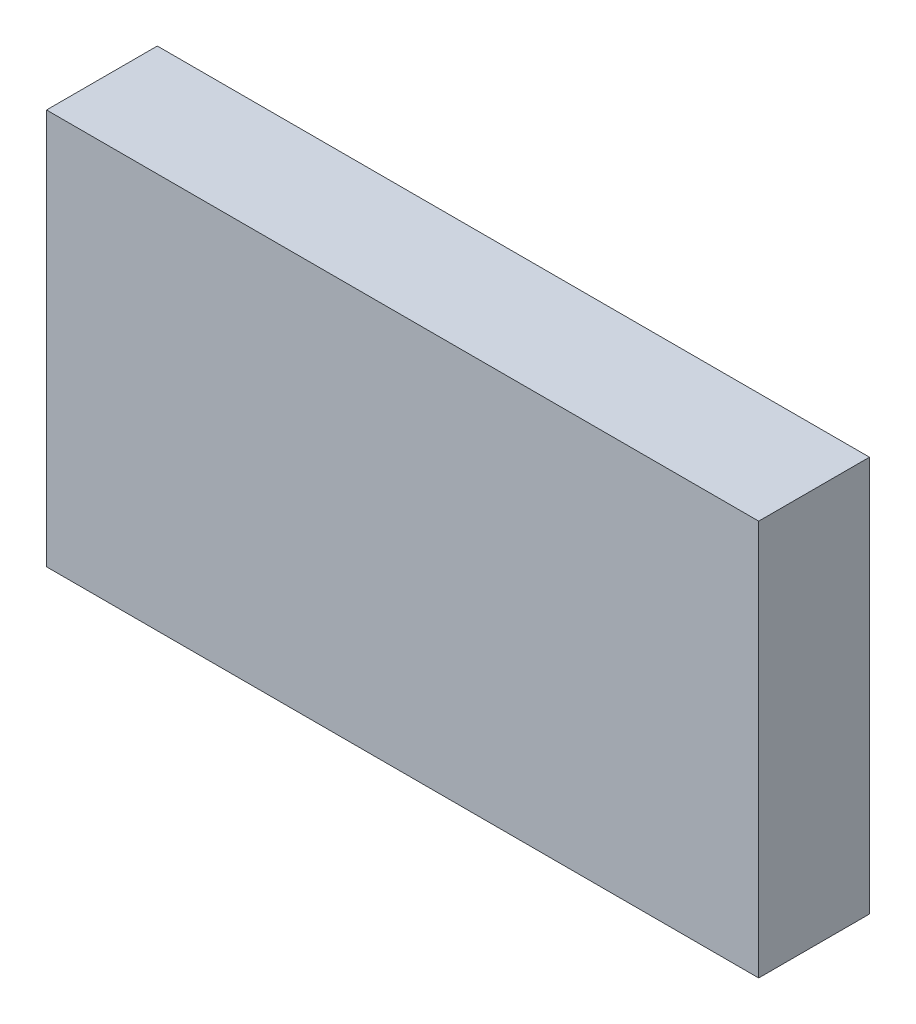
SolidWorks part; units mm, degrees
material "Pine"
ref_plane "Front Plane" through (0, 0, 0) normal (0, 0, 1) x (1, 0, 0)
ref_plane "Top Plane" through (0, 0, 0) normal (0, 1, 0) x (1, 0, 0)
ref_plane "Right Plane" through (0, 0, 0) normal (1, 0, 0) x (0, 0, -1)
sketch "Sketch1" plane through (0, 0, 0) normal (0, 0, 1) x (1, 0, 0)
  line L0 (8932.6508, -5243.5125) -> (10226.1458, -5243.5125)
  line L1 (9086.3208, -4722.0918) -> (10222.9708, -4853.7812)
  line L2 (8914.8708, -6342.0625) -> (10197.5708, -6342.0625)
  line L3 (8914.8708, -5808.6625) -> (10197.5708, -5808.6625)
  line L4 (8919.6333, -5253.0375) -> (10218.2083, -5253.0375)
  line L5 (9134.2633, -4656.1375) -> (9134.2633, -4638.3575)
  line L6 (9091.0833, -4638.3575) -> (9134.2633, -4638.3575)
  line L7 (9091.0833, -4567.2375) -> (9091.0833, -4638.3575)
  line L8 (9134.2633, -4656.1375) -> (9581.3033, -4656.1375)
  line L9 (9091.0833, -4567.2375) -> (9624.4833, -4567.2375)
  line L10 (9581.3033, -4656.1375) -> (9581.3033, -4638.3575)
  line L11 (9581.3033, -4638.3575) -> (9624.4833, -4638.3575)
  line L12 (9624.4833, -4567.2375) -> (9624.4833, -4638.3575)
  line L13 (8932.6508, -5225.7325) -> (9344.9775, -5225.7325)
  line L14 (8932.6508, -5256.2125) -> (8932.6508, -5243.5125)
  line L15 (8911.6958, -5256.2125) -> (8932.6508, -5256.2125)
  line L16 (8914.8708, -4722.0918) -> (9086.3208, -4722.0918)
  line L17 (8911.6958, -4715.5913) -> (8932.6508, -4715.5913)
  line L18 (8914.8708, -6342.0625) -> (8914.8708, -5808.6625)
  line L19 (12082.9917, -4722.0918) -> (10946.3417, -4853.7812)
  line L20 (12236.6617, -5243.5125) -> (10943.1667, -5243.5125)
  line L21 (10951.1042, -5253.0375) -> (12249.6792, -5253.0375)
  line L22 (10838.3917, -5656.2625) -> (11308.2917, -5656.2625)
  line L23 (10838.3917, -5719.7625) -> (11308.2917, -5719.7625)
  line L24 (10838.3917, -5742.5368) -> (11308.2917, -5742.5368)
  line L25 (10806.6417, -6342.0625) -> (11340.0417, -6342.0625)
  line L26 (10803.4667, -6335.7125) -> (11343.2167, -6335.7125)
  line L27 (10803.4667, -6317.9325) -> (11343.2167, -6317.9325)
  line L28 (10943.1667, -5225.7325) -> (11376.4483, -5225.7325)
  line L29 (11506.7292, -4754.5625) -> (10806.6417, -4827.5875)
  line L30 (11506.7292, -4567.2375) -> (11506.7292, -4754.5625)
  line L31 (10806.6417, -4567.2375) -> (10806.6417, -4827.5875)
  line L32 (10806.6417, -4567.2375) -> (11506.7292, -4567.2375)
  line L33 (10235.6708, -6329.3625) -> (10245.1958, -6329.3625)
  line L34 (10245.1958, -6329.3625) -> (10254.7208, -6278.5625)
  line L35 (10302.3458, -6329.3625) -> (10311.8708, -6278.5625)
  line L36 (10302.3458, -6329.3625) -> (10292.8208, -6329.3625)
  line L37 (10245.1958, -5821.3625) -> (10254.7208, -5872.1625)
  line L38 (10235.6708, -5821.3625) -> (10245.1958, -5821.3625)
  line L39 (10292.8208, -5821.3625) -> (10302.3458, -5821.3625)
  line L40 (10302.3458, -5821.3625) -> (10311.8708, -5872.1625)
  line L41 (10235.6708, -5821.3625) -> (10235.6708, -6329.3625)
  line L42 (10254.7208, -5872.1625) -> (10254.7208, -6278.5625)
  line L43 (10311.8708, -5872.1625) -> (10311.8708, -6278.5625)
  line L44 (10292.8208, -5821.3625) -> (10292.8208, -6329.3625)
  line L45 (8932.6508, -5225.7325) -> (8932.6508, -4715.5913)
  line L46 (8911.6958, -4715.5913) -> (8911.6958, -5256.2125)
  line L47 (8914.8708, -5248.275) -> (8914.8708, -4722.0918)
  line L48 (8919.6333, -5253.0375) -> (8914.8708, -5248.275)
  line L49 (8914.8708, -5145.0875) -> (8937.426, -5145.0875)
  line L50 (8914.8708, -5202.2375) -> (8937.426, -5202.2375)
  line L51 (10838.3917, -5656.2625) -> (10838.3917, -5719.7625)
  line L52 (10832.0417, -5736.1868) -> (10856.1717, -5736.1868)
  line L53 (10806.6417, -6342.0625) -> (10806.6417, -5818.7368)
  line L54 (10832.0417, -5649.9125) -> (10856.1717, -5649.9125)
  line L55 (10832.0417, -5726.1125) -> (10856.1717, -5726.1125)
  line L56 (10806.6417, -5818.7368) -> (10833.9015, -5818.7368)
  line L57 (10832.0417, -5806.0442) -> (10851.6815, -5806.0442)
  line L58 (10856.1717, -5801.5541) -> (10856.1717, -5736.1868)
  line L59 (10838.3917, -5814.2467) -> (10838.3917, -5742.5368)
  line L60 (10832.0417, -5806.0442) -> (10832.0417, -5736.1868)
  line L61 (10803.4667, -6317.9325) -> (10803.4667, -6335.7125)
  line L62 (10197.5708, -5808.6625) -> (10197.5708, -6342.0625)
  line L63 (9762.3842, -6348.4125) -> (9762.3842, -5802.3125)
  line L64 (9780.1642, -6348.4125) -> (9762.3842, -6348.4125)
  line L65 (9780.1642, -5802.3125) -> (9780.1642, -6348.4125)
  line L66 (9762.3842, -5802.3125) -> (9780.1642, -5802.3125)
  line L67 (9332.2775, -6348.4125) -> (9332.2775, -5802.3125)
  line L68 (9332.2775, -6348.4125) -> (9350.0575, -6348.4125)
  line L69 (9350.0575, -5802.3125) -> (9350.0575, -6348.4125)
  line L70 (9332.2775, -5802.3125) -> (9350.0575, -5802.3125)
  line L71 (9993.8374, -6061.075) -> (9993.8374, -6045.2418)
  line L72 (9998.5999, -6065.8375) -> (10014.4331, -6065.8375)
  line L73 (9998.5999, -6084.8875) -> (10014.4331, -6084.8875)
  line L74 (9993.8374, -6105.4832) -> (9993.8374, -6089.65)
  line L75 (9974.7874, -6105.4832) -> (9974.7874, -6089.65)
  line L76 (9954.1917, -6084.8875) -> (9970.0249, -6084.8875)
  line L77 (9974.7874, -6061.075) -> (9974.7874, -6045.2418)
  line L78 (9954.1917, -6065.8375) -> (9970.0249, -6065.8375)
  line L79 (10793.9417, -6237.2875) -> (10816.4969, -6237.2875)
  line L80 (10793.9417, -6294.4375) -> (10816.4969, -6294.4375)
  line L81 (10856.1717, -5649.9125) -> (10856.1717, -5726.1125)
  line L82 (10832.0417, -5726.1125) -> (10832.0417, -5649.9125)
  line L83 (10226.1458, -5225.7325) -> (10226.1458, -5243.5125)
  line L84 (10205.1908, -5257.8) -> (10205.1908, -4844.2499)
  line L85 (10230.9083, -4844.2499) -> (10230.9083, -5257.8)
  line L86 (10205.1908, -5257.8) -> (10230.9083, -5257.8)
  line L87 (10205.1908, -4844.2499) -> (10230.9083, -4844.2499)
  line L88 (10946.3417, -5176.8375) -> (10968.8969, -5176.8375)
  line L89 (9349.4676, -5141.9125) -> (9358.2674, -5141.9125)
  line L90 (10946.3417, -5119.6875) -> (10968.8969, -5119.6875)
  line L91 (9929.011, -4660.9635) -> (10066.0807, -4660.9635)
  line L92 (9929.011, -4678.7435) -> (10066.0807, -4678.7435)
  line L93 (10943.1667, -5225.7325) -> (10943.1667, -5243.5125)
  line L94 (10946.3417, -5248.275) -> (10951.1042, -5253.0375)
  line L95 (10946.3417, -5257.8063) -> (10946.3417, -4849.0188)
  line L96 (10964.1217, -5257.8) -> (10964.1217, -4844.2499)
  line L97 (10938.4042, -4844.2499) -> (10938.4042, -5257.8)
  line L98 (10938.4042, -5257.8) -> (10964.1217, -5257.8)
  line L99 (10964.1217, -4844.2499) -> (10938.4042, -4844.2499)
  line L100 (10344.8908, -4560.8875) -> (10369.0208, -4560.8875)
  line L101 (10344.8908, -4560.8875) -> (10369.0208, -4560.8875)
  line L102 (10800.2917, -4560.8875) -> (10824.4217, -4560.8875)
  line L103 (10200.4156, -5119.6875) -> (10222.9708, -5119.6875)
  line L104 (10200.4156, -5176.8375) -> (10222.9708, -5176.8375)
  line L105 (9344.9775, -5146.4026) -> (9344.9775, -5225.7325)
  line L106 (10344.8908, -4560.8875) -> (10344.8908, -4833.9375)
  line L107 (9792.8642, -5225.7325) -> (9792.8642, -5146.4026)
  line L108 (9362.7575, -5225.7325) -> (9775.0842, -5225.7325)
  line L109 (9680.3633, -4761.8396) -> (9680.3633, -4559.9604)
  line L110 (9656.2333, -4559.9604) -> (9680.3633, -4559.9604)
  line L111 (9656.2333, -4761.8396) -> (9680.3633, -4761.8396)
  line L112 (9656.2333, -4761.8396) -> (9656.2333, -4559.9604)
  line L113 (9779.5743, -5141.9125) -> (9788.374, -5141.9125)
  line L114 (10070.5708, -4665.4536) -> (10070.5708, -4674.2534)
  line L115 (9924.5208, -4674.2534) -> (9924.5208, -4665.4536)
  line L116 (12127.4417, -6188.3925) -> (12205.5015, -6188.3925)
  line L117 (12209.9917, -6170.6125) -> (12209.9917, -6183.9024)
  line L118 (9792.8642, -5225.7325) -> (10226.1458, -5225.7325)
  line L119 (9662.5833, -4754.5625) -> (10362.6708, -4827.5875)
  line L120 (9662.5833, -4567.2375) -> (9662.5833, -4754.5625)
  line L121 (10362.6708, -4567.2375) -> (10362.6708, -4827.5875)
  line L122 (9662.5833, -4567.2375) -> (10362.6708, -4567.2375)
  line L123 (10824.4217, -4833.9375) -> (10800.2917, -4833.9375)
  line L124 (10800.2917, -4833.9375) -> (10800.2917, -4560.8875)
  line L125 (10824.4217, -4560.8875) -> (10824.4217, -4833.9375)
  line L126 (10344.8908, -4833.9375) -> (10369.0208, -4833.9375)
  line L127 (10369.0208, -4833.9375) -> (10369.0208, -4560.8875)
  line L128 (10222.9708, -5248.275) -> (10218.2083, -5253.0375)
  line L129 (10222.9708, -5257.8063) -> (10222.9708, -4849.0188)
  line L130 (11734.6544, -5701.375) -> (11739.2301, -5701.375)
  line L131 (9362.7575, -5225.7325) -> (9362.7575, -5146.4026)
  line L132 (9775.0842, -5146.4026) -> (9775.0842, -5225.7325)
  line L133 (11761.3864, -5701.375) -> (11756.8282, -5701.375)
  line L134 (11734.6544, -5693.755) -> (11739.2301, -5693.755)
  line L135 (11761.4039, -5693.755) -> (11756.8282, -5693.755)
  line L136 (11734.6544, -5701.375) -> (11739.2301, -5701.375)
  line L137 (11744.3462, -5721.3024) -> (11744.3462, -5706.4179)
  line L138 (11751.7122, -5721.3024) -> (11751.7122, -5706.4179)
  line L139 (11740.0917, -6170.6125) -> (11740.0917, -6183.9024)
  line L140 (11689.2917, -6188.3925) -> (11822.6417, -6188.3925)
  line L141 (11689.2917, -6348.4093) -> (11689.2917, -6164.2657)
  line L142 (11689.2917, -6164.2657) -> (11746.4417, -6164.2657)
  line L143 (11746.4417, -6164.2657) -> (11746.4417, -6188.3925)
  line L144 (11689.2917, -6164.2657) -> (11746.4417, -6164.2657)
  line L145 (11340.0417, -5818.7368) -> (11340.0417, -6342.0625)
  line L146 (11290.5117, -5726.1125) -> (11314.6417, -5726.1125)
  line L147 (11290.5117, -5649.9125) -> (11290.5117, -5726.1125)
  line L148 (11340.0417, -5818.7368) -> (11312.7818, -5818.7368)
  line L149 (11314.6417, -5806.0442) -> (11295.0018, -5806.0442)
  line L150 (11290.5117, -5801.5541) -> (11290.5117, -5736.1868)
  line L151 (11308.2917, -5814.2467) -> (11308.2917, -5742.5368)
  line L152 (11314.6417, -5806.0442) -> (11314.6417, -5736.1868)
  line L153 (11290.5117, -5736.1868) -> (11314.6417, -5736.1868)
  line L154 (11848.0417, -6267.1325) -> (11962.3417, -6267.1325)
  line L155 (11962.3417, -6267.1325) -> (11962.3417, -6203.6325)
  line L156 (11343.2167, -6317.9325) -> (11343.2167, -6335.7125)
  line L157 (11365.4417, -5656.2625) -> (11365.4417, -5719.7625)
  line L158 (11365.4417, -5656.2625) -> (11479.7417, -5656.2625)
  line L159 (11778.1917, -6071.3937) -> (11802.3217, -6071.3937)
  line L160 (11314.6417, -5726.1125) -> (11314.6417, -5649.9125)
  line L161 (11314.6417, -5649.9125) -> (11290.5117, -5649.9125)
  line L162 (11308.2917, -5719.7625) -> (11308.2917, -5656.2625)
  line L163 (11689.2917, -6348.4093) -> (11713.4217, -6348.4093)
  line L164 (12203.6417, -6164.2657) -> (12260.7917, -6164.2657)
  line L165 (11713.4217, -6348.4093) -> (11713.4217, -6164.2657)
  line L166 (11695.6417, -6342.0625) -> (11695.6417, -6170.6125)
  line L167 (11695.6417, -6048.5337) -> (11699.4517, -6052.3437)
  line L168 (11822.6417, -6292.5325) -> (11822.6417, -6188.3925)
  line L169 (11695.6417, -6342.0625) -> (11695.6417, -6170.6125)
  line L170 (11848.0417, -6203.6325) -> (11962.3417, -6203.6325)
  line L171 (11848.0417, -6203.6325) -> (11848.0417, -6267.1325)
  line L172 (11987.7417, -6267.1325) -> (11987.7417, -6203.6325)
  line L173 (11784.5417, -6077.7437) -> (11784.5417, -6141.2438)
  line L174 (11517.8417, -5656.2625) -> (11632.1417, -5656.2625)
  line L175 (11632.1417, -5656.2625) -> (11632.1417, -5719.7625)
  line L176 (11632.1417, -5719.7625) -> (11517.8417, -5719.7625)
  line L177 (11517.8417, -5719.7625) -> (11517.8417, -5656.2625)
  line L178 (11692.4667, -6028.2137) -> (11692.4667, -6045.9937)
  line L179 (11695.6417, -5979.3188) -> (11718.1969, -5979.3188)
  line L180 (11695.6417, -5922.1687) -> (11718.1969, -5922.1687)
  line L181 (11821.0415, -5722.9375) -> (11821.0415, -5943.6)
  line L182 (11687.7042, -5651.5) -> (11701.9917, -5651.5)
  line L183 (11687.7042, -5651.5) -> (11687.7042, -6055.5251)
  line L184 (11687.7042, -6055.5251) -> (11701.9917, -6055.5251)
  line L185 (11701.9917, -6055.5251) -> (11701.9917, -5651.5)
  line L186 (11695.6417, -6055.2013) -> (11695.6417, -5649.595)
  line L187 (11695.6417, -5656.2625) -> (11695.6417, -6048.5337)
  line L188 (11695.6417, -6170.6125) -> (11740.0917, -6170.6125)
  line L189 (12203.6417, -6164.2657) -> (12203.6417, -6188.3925)
  line L190 (12254.4417, -6342.0625) -> (12254.4417, -6170.6125)
  line L191 (12129.0419, -5943.6) -> (12129.0419, -5722.9375)
  line L192 (12254.4417, -6048.5337) -> (12250.6317, -6052.3437)
  line L193 (12257.6167, -6045.9937) -> (12257.6167, -6028.2137)
  line L194 (12248.0917, -5651.5) -> (12262.3792, -5651.5)
  line L195 (12262.3792, -5651.5) -> (12262.3792, -6055.5251)
  line L196 (12262.3792, -6055.5251) -> (12248.0917, -6055.5251)
  line L197 (12248.0917, -6055.5251) -> (12248.0917, -5651.5)
  line L198 (12254.4417, -6141.2438) -> (12254.4417, -6077.7437)
  line L199 (12236.6617, -6164.2657) -> (12260.7917, -6164.2657)
  line L200 (12102.0417, -6267.1325) -> (11987.7417, -6267.1325)
  line L201 (11330.1865, -6237.2875) -> (11352.7417, -6237.2875)
  line L202 (11330.1865, -6294.4375) -> (11352.7417, -6294.4375)
  line L203 (11474.6617, -5851.8425) -> (11492.4417, -5851.8425)
  line L204 (11474.6617, -5808.6625) -> (11474.6617, -5851.8425)
  line L205 (11403.5417, -5808.6625) -> (11474.6617, -5808.6625)
  line L206 (11492.4417, -5851.8425) -> (11492.4417, -6298.8825)
  line L207 (11403.5417, -6342.0625) -> (11403.5417, -5808.6625)
  line L208 (11474.6617, -6298.8825) -> (11492.4417, -6298.8825)
  line L209 (11474.6617, -6342.0625) -> (11474.6617, -6298.8825)
  line L210 (11403.5417, -6342.0625) -> (11474.6617, -6342.0625)
  line L211 (11619.4417, -5851.8425) -> (11601.6617, -5851.8425)
  line L212 (11601.6617, -5808.6625) -> (11601.6617, -5851.8425)
  line L213 (11530.5417, -5808.6625) -> (11601.6617, -5808.6625)
  line L214 (11619.4417, -5851.8425) -> (11619.4417, -6298.8825)
  line L215 (11530.5417, -6342.0625) -> (11530.5417, -5808.6625)
  line L216 (11619.4417, -6298.8825) -> (11601.6617, -6298.8825)
  line L217 (11601.6617, -6342.0625) -> (11601.6617, -6298.8825)
  line L218 (11530.5417, -6342.0625) -> (11601.6617, -6342.0625)
  line L219 (11479.7417, -5719.7625) -> (11479.7417, -5656.2625)
  line L220 (11365.4417, -5719.7625) -> (11479.7417, -5719.7625)
  line L221 (11778.1917, -6147.5937) -> (11802.3217, -6147.5937)
  line L222 (11802.3217, -6071.3937) -> (11802.3217, -6147.5937)
  line L223 (11778.1917, -6147.5937) -> (11778.1917, -6071.3937)
  line L224 (12254.4417, -5922.1687) -> (12231.8865, -5922.1687)
  line L225 (12254.4417, -5979.3188) -> (12231.8865, -5979.3188)
  line L226 (12254.4417, -6055.2013) -> (12254.4417, -5649.595)
  line L227 (12254.4417, -6048.5337) -> (12254.4417, -5656.2625)
  line L228 (11841.6917, -5702.2873) -> (12108.3917, -5702.2873)
  line L229 (11822.6417, -6292.5325) -> (12127.4417, -6292.5325)
  line L230 (12127.4417, -6292.5325) -> (12127.4417, -6188.3925)
  line L231 (12254.4417, -6170.6125) -> (12209.9917, -6170.6125)
  line L232 (11695.6417, -6342.0625) -> (12254.4417, -6342.0625)
  line L233 (12236.6617, -6348.4093) -> (12260.7917, -6348.4093)
  line L234 (12260.7917, -6348.4093) -> (12260.7917, -6164.2657)
  line L235 (12236.6617, -6348.4093) -> (12236.6617, -6164.2657)
  line L236 (12102.0417, -6203.6325) -> (12102.0417, -6267.1325)
  line L237 (11987.7417, -6203.6325) -> (12102.0417, -6203.6325)
  line L238 (12236.6617, -6147.5937) -> (12236.6617, -6071.3937)
  line L239 (12203.6417, -6188.3925) -> (12260.7917, -6188.3925)
  line L240 (11098.7417, -4665.4536) -> (11098.7417, -4674.2534)
  line L241 (11394.2283, -5146.4026) -> (11394.2283, -5225.7325)
  line L242 (11376.4483, -5225.7325) -> (11376.4483, -5146.4026)
  line L243 (11394.2283, -5225.7325) -> (11806.555, -5225.7325)
  line L244 (11841.6917, -5964.2502) -> (12108.3917, -5964.2502)
  line L245 (12236.6617, -6147.5937) -> (12260.7917, -6147.5937)
  line L246 (12236.6617, -5256.2125) -> (12236.6617, -5243.5125)
  line L247 (12260.7917, -6147.5937) -> (12260.7917, -6071.3937)
  line L248 (12260.7917, -6071.3937) -> (12236.6617, -6071.3937)
  line L249 (12254.4417, -6077.7437) -> (11784.5417, -6077.7437)
  line L250 (11784.5417, -6141.2438) -> (12254.4417, -6141.2438)
  line L252 (12254.4417, -5656.2625) -> (11695.6417, -5656.2625)
  line L253 (11699.4517, -6052.3437) -> (12250.6317, -6052.3437)
  line L254 (11692.4667, -6045.9937) -> (12257.6167, -6045.9937)
  line L255 (11692.4667, -6028.2137) -> (12257.6167, -6028.2137)
  line L256 (11824.335, -5146.4026) -> (11824.335, -5225.7325)
  line L257 (11811.0451, -5141.9125) -> (11819.8449, -5141.9125)
  line L258 (11244.7917, -4674.2534) -> (11244.7917, -4665.4536)
  line L259 (11806.555, -5225.7325) -> (11806.555, -5146.4026)
  line L260 (11488.9492, -4761.8396) -> (11488.9492, -4559.9604)
  line L261 (11488.9492, -4559.9604) -> (11513.0792, -4559.9604)
  line L262 (11488.9492, -4761.8396) -> (11513.0792, -4761.8396)
  line L263 (11513.0792, -4761.8396) -> (11513.0792, -4559.9604)
  line L264 (11240.3015, -4660.9635) -> (11103.2318, -4660.9635)
  line L265 (11103.2318, -4678.7435) -> (11240.3015, -4678.7435)
  line L266 (12236.6617, -5225.7325) -> (12236.6617, -4715.5913)
  line L267 (12257.6167, -4715.5913) -> (12257.6167, -5256.2125)
  line L268 (12254.4417, -5248.275) -> (12254.4417, -4722.0918)
  line L269 (12236.6617, -5225.7325) -> (11824.335, -5225.7325)
  line L270 (12035.0492, -4656.1375) -> (12035.0492, -4638.3575)
  line L271 (12078.2292, -4638.3575) -> (12035.0492, -4638.3575)
  line L272 (12078.2292, -4567.2375) -> (12078.2292, -4638.3575)
  line L273 (12035.0492, -4656.1375) -> (11588.0092, -4656.1375)
  line L274 (11544.8292, -4567.2375) -> (12078.2292, -4567.2375)
  line L275 (11588.0092, -4656.1375) -> (11588.0092, -4638.3575)
  line L276 (11544.8292, -4638.3575) -> (11588.0092, -4638.3575)
  line L277 (11544.8292, -4567.2375) -> (11544.8292, -4638.3575)
  line L278 (12249.6792, -5253.0375) -> (12254.4417, -5248.275)
  line L280 (12257.6167, -5256.2125) -> (12236.6617, -5256.2125)
  line L281 (12231.8865, -5145.0875) -> (12254.4417, -5145.0875)
  line L282 (12231.8865, -5202.2375) -> (12254.4417, -5202.2375)
  line L283 (12236.6617, -4715.5913) -> (12257.6167, -4715.5913)
  line L284 (12082.9917, -4722.0918) -> (12254.4417, -4722.0918)
  line L285 (11380.9385, -5141.9125) -> (11389.7382, -5141.9125)
  circle A0 centre (8923.7608, -4778.9042) radius 1.5875
  circle A1 centre (9062.6598, -4736.3765) radius 2.3685
  circle A2 centre (9051.3958, -6281.7375) radius 22.225
  circle A3 centre (9083.1458, -6249.9875) radius 1.5875
  circle A4 centre (9083.1458, -6313.4875) radius 1.5875
  circle A5 centre (9019.6458, -6249.9875) radius 1.5875
  circle A6 centre (9019.6458, -6313.4875) radius 1.5875
  circle A7 centre (8972.3383, -5202.2375) radius 1.5875
  circle A8 centre (8923.7608, -5015.9708) radius 1.5875
  circle A9 centre (8923.7608, -5134.5042) radius 1.5875
  circle A10 centre (9054.5708, -5234.6225) radius 1.5875
  circle A11 centre (8923.7608, -4897.4375) radius 1.5875
  circle A12 centre (8972.3383, -5087.9375) radius 1.5875
  circle A13 centre (8972.3383, -5145.0875) radius 1.5875
  circle A14 centre (10847.2817, -5668.9625) radius 1.5875
  circle A15 centre (10847.2817, -5707.0625) radius 1.5875
  circle A16 centre (10847.2817, -5755.2368) radius 1.5875
  circle A17 centre (10851.4092, -6237.2875) radius 1.5875
  circle A18 centre (10851.4092, -6294.4375) radius 1.5875
  circle A19 centre (10847.2817, -5793.3442) radius 1.5875
  arc A20 (10833.9015, -5818.7368) -> (10838.3917, -5814.2467) centre (10836.1466, -5816.4918) ccw
  arc A21 (10851.6815, -5806.0442) -> (10856.1717, -5801.5541) centre (10853.9266, -5803.7992) ccw
  circle A22 centre (10882.8417, -6040.4375) radius 1.5875
  circle A23 centre (10882.8417, -6218.2375) radius 1.5875
  circle A24 centre (10882.8417, -5862.6375) radius 1.5875
  circle A25 centre (10908.2417, -6326.8225) radius 1.5875
  circle A26 centre (10908.2417, -6326.8225) radius 1.5875
  circle A27 centre (10851.4092, -6180.1375) radius 1.5875
  circle A28 centre (10815.5317, -4783.4231) radius 1.5875
  circle A29 centre (10815.5317, -4696.9488) radius 1.5875
  circle A30 centre (10815.5317, -4610.4746) radius 1.5875
  circle A31 centre (10979.1323, -4867.0082) radius 2.3685
  circle A32 centre (10190.1802, -4867.0082) radius 2.3685
  circle A33 centre (10955.2317, -4929.9812) radius 1.5875
  circle A34 centre (10955.2317, -5031.5812) radius 1.5875
  circle A35 centre (10214.0808, -4929.9812) radius 1.5875
  circle A36 centre (10214.0808, -5031.5812) radius 1.5875
  circle A37 centre (9341.1675, -6265.8625) radius 1.5875
  circle A38 centre (9771.2742, -5884.8625) radius 1.5875
  circle A39 centre (9771.2742, -6138.8625) radius 1.5875
  circle A40 centre (9771.2742, -6011.8625) radius 1.5875
  arc A41 (10036.2287, -6113.8083) -> (10051.3426, -6111.6033) centre (10042.9639, -6107.0732) ccw
  arc A42 (10051.3426, -6111.6033) -> (10051.3426, -6039.1217) centre (9984.3124, -6075.3625) ccw
  arc A43 (10051.3426, -6039.1217) -> (10036.2287, -6036.9167) centre (10042.9639, -6043.6518) ccw
  arc A44 (10034.5851, -6102.5431) -> (10034.5851, -6048.1819) centre (9984.3124, -6075.3625) ccw
  arc A45 (10034.5851, -6102.5431) -> (10036.2287, -6113.8083) centre (10042.9639, -6107.0732) ccw
  arc A46 (10036.2287, -6036.9167) -> (10034.5851, -6048.1819) centre (10042.9639, -6043.6518) ccw
  arc A47 (9945.8666, -6127.2787) -> (9948.0717, -6142.3927) centre (9952.6018, -6134.0139) ccw
  arc A48 (9948.0717, -6142.3927) -> (10020.5532, -6142.3927) centre (9984.3124, -6075.3625) ccw
  arc A49 (10020.5532, -6142.3927) -> (10022.7583, -6127.2787) centre (10016.0231, -6134.0139) ccw
  arc A50 (9957.1319, -6125.6352) -> (10011.493, -6125.6352) centre (9984.3124, -6075.3625) ccw
  arc A51 (9957.1319, -6125.6352) -> (9945.8666, -6127.2787) centre (9952.6018, -6134.0139) ccw
  arc A52 (10022.7583, -6127.2787) -> (10011.493, -6125.6352) centre (10016.0231, -6134.0139) ccw
  arc A53 (9932.3962, -6036.9167) -> (9917.2822, -6039.1217) centre (9925.661, -6043.6518) ccw
  arc A54 (9917.2822, -6039.1217) -> (9917.2822, -6111.6033) centre (9984.3124, -6075.3625) ccw
  arc A55 (9917.2822, -6111.6033) -> (9932.3962, -6113.8083) centre (9925.661, -6107.0732) ccw
  arc A56 (9934.0398, -6048.1819) -> (9934.0398, -6102.5431) centre (9984.3124, -6075.3625) ccw
  arc A57 (9934.0398, -6048.1819) -> (9932.3962, -6036.9167) centre (9925.661, -6043.6518) ccw
  arc A58 (9932.3962, -6113.8083) -> (9934.0398, -6102.5431) centre (9925.661, -6107.0732) ccw
  arc A59 (9945.8666, -6023.4463) -> (9957.1319, -6025.0898) centre (9952.6018, -6016.7111) ccw
  arc A60 (10011.493, -6025.0898) -> (10022.7583, -6023.4463) centre (10016.0231, -6016.7111) ccw
  arc A61 (10011.493, -6025.0898) -> (9957.1319, -6025.0898) centre (9984.3124, -6075.3625) ccw
  arc A62 (9948.0717, -6008.3323) -> (9945.8666, -6023.4463) centre (9952.6018, -6016.7111) ccw
  arc A63 (10020.5532, -6008.3323) -> (9948.0717, -6008.3323) centre (9984.3124, -6075.3625) ccw
  arc A64 (10022.7583, -6023.4463) -> (10020.5532, -6008.3323) centre (10016.0231, -6016.7111) ccw
  arc A65 (10005.0943, -6187.7574) -> (10096.7073, -6096.1443) centre (9984.3124, -6075.3625) ccw
  arc A66 (9993.8374, -6178.3911) -> (10005.0943, -6187.7574) centre (10003.3624, -6178.3911) ccw
  arc A67 (10001.6306, -6169.0249) -> (10077.9748, -6092.6807) centre (9984.3124, -6075.3625) ccw
  arc A68 (10087.3411, -6084.8875) -> (10077.9748, -6092.6807) centre (10087.3411, -6094.4125) ccw
  arc A69 (10001.6306, -6169.0249) -> (9993.8374, -6178.3911) centre (10003.3624, -6178.3911) ccw
  arc A70 (9963.5306, -6187.7574) -> (9974.7874, -6178.3911) centre (9965.2624, -6178.3911) ccw
  arc A71 (9871.9176, -6096.1443) -> (9963.5306, -6187.7574) centre (9984.3124, -6075.3625) ccw
  arc A72 (9881.2838, -6084.8875) -> (9871.9176, -6096.1443) centre (9881.2838, -6094.4125) ccw
  arc A73 (9890.65, -6092.6807) -> (9966.9943, -6169.0249) centre (9984.3124, -6075.3625) ccw
  arc A74 (9974.7874, -6178.3911) -> (9966.9943, -6169.0249) centre (9965.2624, -6178.3911) ccw
  arc A75 (9890.65, -6092.6807) -> (9881.2838, -6084.8875) centre (9881.2838, -6094.4125) ccw
  arc A76 (9871.9176, -6054.5807) -> (9881.2838, -6065.8375) centre (9881.2838, -6056.3125) ccw
  arc A77 (9963.5306, -5962.9676) -> (9871.9176, -6054.5807) centre (9984.3124, -6075.3625) ccw
  arc A78 (9974.7874, -5972.3339) -> (9963.5306, -5962.9676) centre (9965.2624, -5972.3339) ccw
  arc A79 (9966.9943, -5981.7001) -> (9890.65, -6058.0443) centre (9984.3124, -6075.3625) ccw
  arc A80 (9881.2838, -6065.8375) -> (9890.65, -6058.0443) centre (9881.2838, -6056.3125) ccw
  arc A81 (9966.9943, -5981.7001) -> (9974.7874, -5972.3339) centre (9965.2624, -5972.3339) ccw
  arc A82 (10077.9748, -6058.0443) -> (10087.3411, -6065.8375) centre (10087.3411, -6056.3125) ccw
  arc A83 (9993.8374, -5972.3339) -> (10001.6306, -5981.7001) centre (10003.3624, -5972.3339) ccw
  arc A84 (10077.9748, -6058.0443) -> (10001.6306, -5981.7001) centre (9984.3124, -6075.3625) ccw
  arc A85 (10087.3411, -6065.8375) -> (10096.7073, -6054.5807) centre (10087.3411, -6056.3125) ccw
  arc A86 (10096.7073, -6054.5807) -> (10005.0943, -5962.9676) centre (9984.3124, -6075.3625) ccw
  arc A87 (10005.0943, -5962.9676) -> (9993.8374, -5972.3339) centre (10003.3624, -5972.3339) ccw
  arc A88 (10014.4331, -6065.8375) -> (10018.7361, -6059.0339) centre (10014.4331, -6061.075) ccw
  arc A89 (10018.7361, -6059.0339) -> (10000.641, -6040.9388) centre (9984.3124, -6075.3625) ccw
  arc A90 (10000.641, -6040.9388) -> (9993.8374, -6045.2418) centre (9998.5999, -6045.2418) ccw
  arc A91 (9993.8374, -6061.075) -> (9998.5999, -6065.8375) centre (9998.5999, -6061.075) ccw
  arc A92 (9993.8374, -6105.4832) -> (10000.641, -6109.7862) centre (9998.5999, -6105.4832) ccw
  arc A93 (10000.641, -6109.7862) -> (10018.7361, -6091.6911) centre (9984.3124, -6075.3625) ccw
  arc A94 (10018.7361, -6091.6911) -> (10014.4331, -6084.8875) centre (10014.4331, -6089.65) ccw
  arc A95 (9998.5999, -6084.8875) -> (9993.8374, -6089.65) centre (9998.5999, -6089.65) ccw
  arc A96 (9954.1917, -6084.8875) -> (9949.8888, -6091.6911) centre (9954.1917, -6089.65) ccw
  arc A97 (9949.8888, -6091.6911) -> (9967.9839, -6109.7862) centre (9984.3124, -6075.3625) ccw
  arc A98 (9967.9839, -6109.7862) -> (9974.7874, -6105.4832) centre (9970.0249, -6105.4832) ccw
  arc A99 (9974.7874, -6089.65) -> (9970.0249, -6084.8875) centre (9970.0249, -6089.65) ccw
  arc A100 (9970.0249, -6065.8375) -> (9974.7874, -6061.075) centre (9970.0249, -6061.075) ccw
  arc A101 (9949.8888, -6059.0339) -> (9954.1917, -6065.8375) centre (9954.1917, -6061.075) ccw
  arc A102 (9967.9839, -6040.9388) -> (9949.8888, -6059.0339) centre (9984.3124, -6075.3625) ccw
  arc A103 (9974.7874, -6045.2418) -> (9967.9839, -6040.9388) centre (9970.0249, -6045.2418) ccw
  arc A104 (10096.7073, -6096.1443) -> (10087.3411, -6084.8875) centre (10087.3411, -6094.4125) ccw
  circle A105 centre (9771.2742, -6265.8625) radius 1.5875
  circle A106 centre (9341.1675, -5884.8625) radius 1.5875
  circle A107 centre (9341.1675, -6138.8625) radius 1.5875
  circle A108 centre (9341.1675, -6011.8625) radius 1.5875
  circle A109 centre (11037.2315, -4887.5494) radius 15.0812
  arc A110 (9349.4676, -5141.9125) -> (9344.9775, -5146.4026) centre (9347.2226, -5144.1576) ccw
  arc A111 (9362.7575, -5146.4026) -> (9358.2674, -5141.9125) centre (9360.5124, -5144.1576) ccw
  circle A112 centre (9946.7458, -4669.8535) radius 1.5875
  arc A113 (9924.5208, -4674.2534) -> (9929.011, -4678.7435) centre (9926.7659, -4676.4984) ccw
  circle A114 centre (11003.8092, -5176.8375) radius 1.5875
  circle A115 centre (11003.8092, -5119.6875) radius 1.5875
  circle A116 centre (10353.7808, -4696.9488) radius 1.5875
  circle A117 centre (10353.7808, -4610.4746) radius 1.5875
  circle A118 centre (10353.7808, -4783.4231) radius 1.5875
  circle A119 centre (11003.8092, -5062.5375) radius 1.5875
  circle A120 centre (9353.8675, -5160.9625) radius 1.5875
  circle A121 centre (9638.7708, -5234.6225) radius 1.5875
  circle A122 centre (9671.4733, -4724.1144) radius 1.5875
  circle A123 centre (9671.4733, -4661.3637) radius 1.5875
  circle A124 centre (9671.4733, -4598.6129) radius 1.5875
  arc A125 (9792.8642, -5146.4026) -> (9788.374, -5141.9125) centre (9790.6191, -5144.1576) ccw
  arc A126 (9779.5743, -5141.9125) -> (9775.0842, -5146.4026) centre (9777.3292, -5144.1576) ccw
  circle A127 centre (10048.3458, -4669.8535) radius 1.5875
  arc A128 (10070.5708, -4665.4536) -> (10066.0807, -4660.9635) centre (10068.3258, -4663.2086) ccw
  arc A129 (10066.0807, -4678.7435) -> (10070.5708, -4674.2534) centre (10068.3258, -4676.4984) ccw
  circle A130 centre (9997.5458, -4669.8535) radius 1.5875
  arc A131 (9929.011, -4660.9635) -> (9924.5208, -4665.4536) centre (9926.7659, -4663.2086) ccw
  circle A132 centre (10132.081, -4887.5494) radius 15.0812
  circle A133 centre (10165.5033, -5176.8375) radius 1.5875
  circle A134 centre (10165.5033, -5119.6875) radius 1.5875
  circle A135 centre (9486.3708, -5234.6225) radius 1.5875
  circle A136 centre (10165.5033, -5062.5375) radius 1.5875
  circle A137 centre (9206.9708, -5234.6225) radius 1.5875
  circle A138 centre (10070.5708, -5234.6225) radius 1.5875
  circle A139 centre (9918.1708, -5234.6225) radius 1.5875
  circle A140 centre (9783.9742, -5160.9625) radius 1.5875
  circle A141 centre (9783.9742, -5193.9825) radius 1.5875
  circle A142 centre (9353.8675, -5193.9825) radius 1.5875
  circle A143 centre (11073.3417, -6326.8225) radius 1.5875
  circle A144 centre (11073.3417, -6326.8225) radius 1.5875
  circle A145 centre (11295.2742, -6180.1375) radius 1.5875
  circle A146 centre (11295.2742, -6294.4375) radius 1.5875
  circle A147 centre (11295.2742, -6237.2875) radius 1.5875
  circle A148 centre (11975.0417, -5692.775) radius 3.4925
  circle A149 centre (11263.8417, -5862.6375) radius 1.5875
  arc A150 (11739.2301, -5701.375) -> (11744.3462, -5706.4179) centre (11748.0292, -5697.565) ccw
  arc A151 (11751.7122, -5706.4179) -> (11756.8282, -5701.375) centre (11748.0292, -5697.565) ccw
  arc A152 (11744.3462, -5721.3024) -> (11751.7122, -5721.3024) centre (11748.0292, -5725.505) ccw
  arc A153 (11734.6544, -5693.755) -> (11724.9787, -5697.565) centre (11730.5667, -5697.565) ccw
  arc A154 (11756.8282, -5693.755) -> (11739.2301, -5693.755) centre (11748.0292, -5697.565) ccw
  arc A155 (11724.9787, -5697.565) -> (11734.6544, -5701.375) centre (11730.5667, -5697.565) ccw
  arc A156 (11761.3864, -5701.375) -> (11771.0797, -5697.565) centre (11765.4842, -5697.565) ccw
  arc A157 (11771.0797, -5697.565) -> (11761.4039, -5693.755) centre (11765.4917, -5697.565) ccw
  arc A158 (11740.0917, -6183.9024) -> (11744.5818, -6188.3925) centre (11742.3367, -6186.1474) ccw
  arc A159 (12205.5015, -6188.3925) -> (12209.9917, -6183.9024) centre (12207.7466, -6186.1474) ccw
  circle A160 centre (11299.4017, -5793.3442) radius 1.5875
  arc A161 (11308.2917, -5814.2467) -> (11312.7818, -5818.7368) centre (11310.5367, -5816.4918) ccw
  arc A162 (11290.5117, -5801.5541) -> (11295.0018, -5806.0442) centre (11292.7567, -5803.7992) ccw
  circle A163 centre (11704.5317, -6314.149) radius 1.5875
  circle A164 centre (11748.9817, -6208.7125) radius 1.5875
  circle A165 centre (11263.8417, -6218.2375) radius 1.5875
  circle A166 centre (11263.8417, -6040.4375) radius 1.5875
  circle A167 centre (11238.4417, -6326.8225) radius 1.5875
  circle A168 centre (11238.4417, -6326.8225) radius 1.5875
  circle A169 centre (11299.4017, -5668.9625) radius 1.5875
  circle A170 centre (11299.4017, -5707.0625) radius 1.5875
  circle A171 centre (11726.7567, -6179.5025) radius 1.5875
  circle A172 centre (11704.5317, -6199.3198) radius 1.5875
  circle A173 centre (11748.9817, -6272.2125) radius 1.5875
  circle A174 centre (11704.5317, -6256.7344) radius 1.5875
  circle A175 centre (11299.4017, -5755.2368) radius 1.5875
  circle A176 centre (11913.4467, -6301.4225) radius 1.5875
  circle A177 centre (11790.2567, -6301.4225) radius 1.5875
  circle A178 centre (11793.4317, -6128.5437) radius 1.5875
  circle A179 centre (11753.1092, -5865.0188) radius 1.5875
  circle A180 centre (11809.9417, -6037.1038) radius 1.5875
  circle A181 centre (11809.9417, -6037.1038) radius 1.5875
  circle A182 centre (11753.1092, -5922.1687) radius 1.5875
  circle A183 centre (11975.0417, -5973.7625) radius 3.4925
  circle A184 centre (11975.0417, -6037.1038) radius 1.5875
  circle A185 centre (11753.1092, -5979.3188) radius 1.5875
  circle A186 centre (11975.0417, -6037.1038) radius 1.5875
  arc A187 (11841.6917, -5702.2873) -> (11821.0415, -5722.9375) centre (11841.6917, -5722.9375) ccw
  circle A188 centre (11811.5292, -5833.2687) radius 3.4925
  arc A189 (11821.0415, -5943.6) -> (11841.6917, -5964.2502) centre (11841.6917, -5943.6) ccw
  circle A190 centre (12196.9742, -5865.0188) radius 1.5875
  arc A191 (12129.0419, -5722.9375) -> (12108.3917, -5702.2873) centre (12108.3917, -5722.9375) ccw
  circle A192 centre (12036.6367, -6301.4225) radius 1.5875
  circle A193 centre (12159.8267, -6301.4225) radius 1.5875
  circle A194 centre (12138.5542, -5833.2687) radius 3.4925
  circle A195 centre (12197.2917, -5761.0375) radius 15.0812
  circle A196 centre (11793.4317, -6090.4437) radius 1.5875
  circle A197 centre (12196.9742, -5922.1687) radius 1.5875
  arc A198 (12108.3917, -5964.2502) -> (12129.0419, -5943.6) centre (12108.3917, -5943.6) ccw
  circle A199 centre (12196.9742, -5979.3188) radius 1.5875
  circle A200 centre (12201.1017, -6272.2125) radius 1.5875
  circle A201 centre (12245.5517, -6314.149) radius 1.5875
  circle A202 centre (12245.5517, -6256.7344) radius 1.5875
  circle A203 centre (12201.1017, -6208.7125) radius 1.5875
  circle A204 centre (12223.3267, -6179.5025) radius 1.5875
  circle A205 centre (12245.5517, -6199.3198) radius 1.5875
  circle A206 centre (11171.7667, -4669.8535) radius 1.5875
  circle A207 centre (11222.5667, -4669.8535) radius 1.5875
  arc A208 (11240.3015, -4678.7435) -> (11244.7917, -4674.2534) centre (11242.5466, -4676.4984) ccw
  circle A209 centre (11385.3383, -5193.9825) radius 1.5875
  circle A210 centre (12106.6527, -4736.3765) radius 2.3685
  circle A211 centre (12140.1417, -6037.1038) radius 1.5875
  circle A212 centre (12140.1417, -6037.1038) radius 1.5875
  circle A213 centre (12245.5517, -6090.4437) radius 1.5875
  circle A214 centre (12245.5517, -6128.5437) radius 1.5875
  circle A215 centre (11385.3383, -5160.9625) radius 1.5875
  arc A216 (11824.335, -5146.4026) -> (11819.8449, -5141.9125) centre (11822.0899, -5144.1576) ccw
  arc A217 (11811.0451, -5141.9125) -> (11806.555, -5146.4026) centre (11808.8001, -5144.1576) ccw
  circle A218 centre (11815.445, -5193.9825) radius 1.5875
  circle A219 centre (11815.445, -5160.9625) radius 1.5875
  circle A220 centre (11530.5417, -5234.6225) radius 1.5875
  circle A221 centre (11962.3417, -5234.6225) radius 1.5875
  arc A222 (11244.7917, -4665.4536) -> (11240.3015, -4660.9635) centre (11242.5466, -4663.2086) ccw
  circle A223 centre (11682.9417, -5234.6225) radius 1.5875
  circle A224 centre (11497.8392, -4724.1144) radius 1.5875
  circle A225 centre (11497.8392, -4661.3637) radius 1.5875
  circle A226 centre (11497.8392, -4598.6129) radius 1.5875
  circle A227 centre (11120.9667, -4669.8535) radius 1.5875
  arc A228 (11103.2318, -4660.9635) -> (11098.7417, -4665.4536) centre (11100.9867, -4663.2086) ccw
  arc A229 (11098.7417, -4674.2534) -> (11103.2318, -4678.7435) centre (11100.9867, -4676.4984) ccw
  circle A230 centre (12196.9742, -5202.2375) radius 1.5875
  circle A231 centre (12245.5517, -5015.9708) radius 1.5875
  circle A232 centre (12245.5517, -5134.5042) radius 1.5875
  circle A233 centre (12114.7417, -5234.6225) radius 1.5875
  circle A234 centre (12245.5517, -4897.4375) radius 1.5875
  circle A235 centre (12245.5517, -4778.9042) radius 1.5875
  circle A236 centre (12196.9742, -5087.9375) radius 1.5875
  circle A237 centre (12196.9742, -5145.0875) radius 1.5875
  circle A238 centre (11098.7417, -5234.6225) radius 1.5875
  circle A239 centre (11251.1417, -5234.6225) radius 1.5875
  arc A240 (11380.9385, -5141.9125) -> (11376.4483, -5146.4026) centre (11378.6934, -5144.1576) ccw
  arc A241 (11394.2283, -5146.4026) -> (11389.7382, -5141.9125) centre (11391.9833, -5144.1576) ccw
sketch "Sketch2" plane through (0, 0, 0) normal (0, 0, 1) x (1, 0, 0)
  line L0 (11517.8417, -5656.2625) -> (11517.8417, -5719.7625)
  line L1 (11517.8417, -5719.7625) -> (11632.1417, -5719.7625)
  line L2 (11632.1417, -5719.7625) -> (11632.1417, -5656.2625)
  line L3 (11632.1417, -5656.2625) -> (11517.8417, -5656.2625)
extrude "Extrude1" add sketch "Sketch2" against normal blind 17.78
